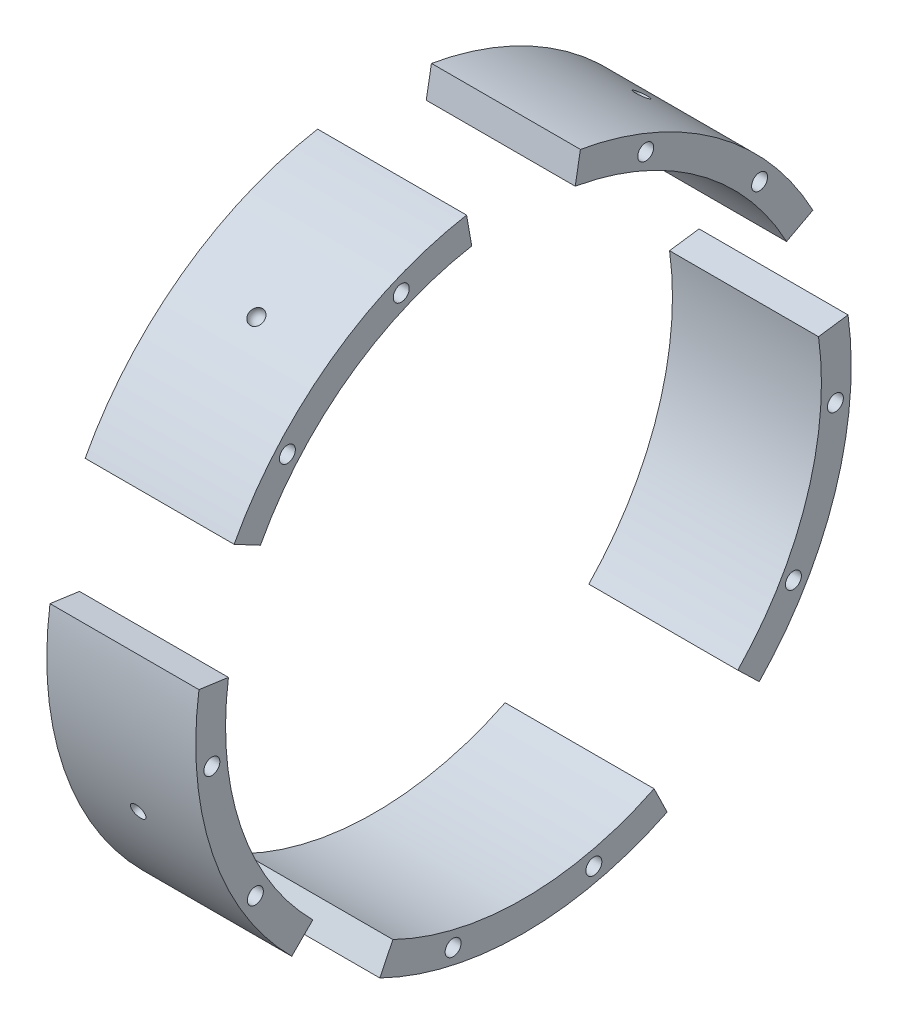
SolidWorks part; units mm, degrees
ref_plane "Front Plane" through (0, 0, 0) normal (0, 0, 1) x (1, 0, 0)
ref_plane "Top Plane" through (0, 0, 0) normal (0, 1, 0) x (1, 0, 0)
ref_plane "Right Plane" through (0, 0, 0) normal (1, 0, 0) x (0, 0, -1)
sketch "Sketch1" plane through (0, 0, 0) normal (1, 0, 0) x (0, 0, -1)
  line L1 (87.6742, -179.7588) -> (96.4417, -197.7347)
  line L2 (143.868, -138.9317) -> (158.2548, -152.8248)
  line L4 (198.0536, 27.8346) -> (217.859, 30.6181)
  line L5 (176.5895, 93.8943) -> (194.2485, 103.2837)
  line L7 (34.7296, 196.9616) -> (38.2026, 216.6577)
  line L8 (-34.7296, 196.9616) -> (-38.2026, 216.6577)
  line L10 (-176.5895, 93.8943) -> (-194.2485, 103.2837)
  line L11 (-198.0536, 27.8346) -> (-217.859, 30.6181)
  line L13 (-141.4214, -141.4214) -> (-155.5635, -155.5635)
  line L14 (-87.6742, -179.7588) -> (-96.4417, -197.7347)
  arc A0 (143.868, -138.9317) -> (198.0536, 27.8346) centre (0, 0) ccw
  arc A1 (158.2548, -152.8248) -> (217.859, 30.6181) centre (0, 0) ccw
  arc A2 (194.2485, 103.2837) -> (38.2026, 216.6577) centre (0, 0) ccw
  arc A3 (176.5895, 93.8943) -> (34.7296, 196.9616) centre (0, 0) ccw
  arc A4 (-38.2026, 216.6577) -> (-194.2485, 103.2837) centre (0, 0) ccw
  arc A5 (-34.7296, 196.9616) -> (-176.5895, 93.8943) centre (0, 0) ccw
  arc A6 (-198.0536, 27.8346) -> (-141.4214, -141.4214) centre (0, 0) ccw
  arc A7 (-217.859, 30.6181) -> (-155.5635, -155.5635) centre (0, 0) ccw
  arc A8 (-87.6742, -179.7588) -> (87.6742, -179.7588) centre (0, 0) ccw
  arc A9 (-96.4417, -197.7347) -> (96.4417, -197.7347) centre (0, 0) ccw
  point P8 (0, -220)
  point P11 (-208.6312, -69.807)
  point P14 (-129.3128, 177.9837)
  point P17 (129.3128, 177.9837)
  point P19 (209.2324, -67.9837)
  point P26 (87.6742, -179.7588)
  point P27 (143.868, -138.9317)
  point P29 (198.0536, 27.8346)
  point P30 (176.5895, 93.8943)
  point P32 (34.7296, 196.9616)
  point P33 (-34.7296, 196.9616)
extrude "Boss-Extrude1" add sketch "Sketch1" along normal blind 100
ref_plane "Plane1" through (0, 177.9837, 129.3128) normal (0, 0.809, 0.5878) x (1, 0, 0)
ref_plane "Plane2" through (0, -69.807, 208.6312) normal (0, -0.3173, 0.9483) x (1, 0, 0)
ref_plane "Plane3" through (0, -67.9837, -209.2324) normal (0, -0.309, -0.9511) x (-1, 0, 0)
ref_plane "Plane4" through (0, -220, 0) normal (0, -1, 0) x (-1, 0, 0)
ref_plane "Plane5" through (0, 177.9837, -129.3128) normal (0, 0.809, -0.5878) x (1, 0, 0)
sketch "Sketch2" plane through (0, 177.9837, 129.3128) normal (0, 0.809, 0.5878) x (1, 0, 0)
  line L0 (45, 0) -> (55, 0)
  arc A0 (55, 0) -> (45, 0) centre (50, 0) ccw
  point P6 (50, 0)
sketch "Sketch4" plane through (0, 177.9837, -129.3128) normal (0, 0.809, -0.5878) x (1, 0, 0)
  line L0 (45, 0) -> (55, 0)
  arc A0 (55, 0) -> (45, 0) centre (50, 0) ccw
  point P6 (50, 0)
sketch "Sketch5" plane through (0, -67.9837, -209.2324) normal (0, -0.309, -0.9511) x (-1, 0, 0)
  line L0 (-55, 0) -> (-45, 0)
  arc A0 (-45, 0) -> (-55, 0) centre (-50, 0) ccw
  point P5 (-50, 0)
sketch "Sketch6" plane through (0, -220, 0) normal (0, -1, 0) x (-1, 0, 0)
  line L0 (-55, 0) -> (-45, 0)
  arc A0 (-45, 0) -> (-55, 0) centre (-50, 0) cw
  point P5 (-50, 0)
sketch "Sketch7" plane through (0, -69.807, 208.6312) normal (0, -0.3173, 0.9483) x (1, 0, 0)
  line L0 (45, 0) -> (55, 0)
  arc A0 (55, 0) -> (45, 0) centre (50, 0) ccw
  point P5 (50, 0)
revolve "Cut-Revolve1" cut sketch "Sketch2" angle 360 about L0
revolve "Cut-Revolve2" cut sketch "Sketch4" angle 360 about L0
revolve "Cut-Revolve3" cut sketch "Sketch5" angle 360 about L0
revolve "Cut-Revolve4" cut sketch "Sketch6" angle 360 about L0
revolve "Cut-Revolve5" cut sketch "Sketch7" angle 360 about L0
ref_plane "Plane6" through (110, 0, 0) normal (1, 0, 0) x (0, 0, -1)
sketch "Sketch8" plane through (110, 0, 0) normal (1, 0, 0) x (0, 0, -1)
  line L0 (-129.3128, 177.9837) -> (-117.5571, 161.8034)
  line L1 (117.5571, 161.8034) -> (129.3128, 177.9837)
  line L2 (-190.2113, -61.8034) -> (-209.2324, -67.9837)
  line L3 (190.2113, -61.8034) -> (209.2324, -67.9837)
  line L4 (0, -200) -> (0, -220)
  line L5 (-150.9419, 131.2118) -> (-166.0361, 144.333)
  line L6 (-78.1462, 184.101) -> (-85.9608, 202.5111)
  line L7 (150.9419, 131.2118) -> (166.0361, 144.333)
  line L8 (78.1462, 184.101) -> (85.9608, 202.5111)
  line L9 (199.3447, -16.1766) -> (219.4045, -16.1766)
  line L10 (172.2044, -100.0777) -> (190.2113, -110.5426)
  line L11 (44.9902, -194.874) -> (49.4892, -214.3614)
  line L12 (-44.9902, -194.874) -> (-49.4892, -214.3614)
  line L13 (-171.4335, -103.0076) -> (-188.5768, -113.3084)
  line L14 (-199.2389, -17.4311) -> (-219.1628, -19.1743)
  arc A5 (-87.6742, -179.7588) -> (87.6742, -179.7588) centre (0, 0) ccw construction
  arc A6 (143.868, -138.9317) -> (198.0536, 27.8346) centre (0, 0) ccw construction
  arc A7 (176.5895, 93.8943) -> (34.7296, 196.9616) centre (0, 0) ccw construction
  arc A8 (-34.7296, 196.9616) -> (-176.5895, 93.8943) centre (0, 0) ccw construction
  arc A9 (-198.0536, 27.8346) -> (-141.4214, -141.4214) centre (0, 0) ccw construction
  circle A10 centre (0, 0) radius 220
  point P0 (-123.4349, 169.8936)
  point P1 (123.4349, 169.8936)
  point P3 (199.7219, -64.8936)
  point P5 (-117.5571, 161.8034)
  point P10 (117.5571, 161.8034)
  point P11 (190.2113, -61.8034)
  point P12 (0, -200)
  point P13 (-190.2113, -61.8034)
  point P19 (0, -210)
  point P20 (-199.7219, -64.8936)
  point P27 (-44.9902, -194.874)
  point P44 (-158.489, 137.7724)
  point P45 (-82.0535, 193.306)
  point P46 (82.0535, 193.306)
  point P47 (158.489, 137.7724)
  point P48 (209.3746, -16.1766)
  point P49 (44.9902, -194.874)
  point P53 (172.2044, -100.0777)
  point P54 (-171.4335, -103.0076)
  point P55 (-199.2389, -17.4311)
  point P59 (-150.9419, 131.2118)
  point P60 (-78.1462, 184.101)
  point P64 (78.1462, 184.101)
  point P65 (150.9419, 131.2118)
  point P69 (199.3447, -16.1766)
  point P70 (181.2078, -105.3102)
  point P74 (47.2397, -204.6177)
  point P75 (-47.2397, -204.6177)
  point P76 (-180.0051, -108.158)
  point P77 (-209.2009, -18.3027)
hole_wizard "1/2-13 Tapped Hole3" positions "3DSketch4" profile "Sketch13" tap size "1/2-13" standard "ANSI Inch"
sketch3d "3DSketch4"
  point P0 (110, 137.7724, 158.489)
  point P3 (110, 193.306, 82.0535)
  point P6 (110, -18.3027, 209.2009)
  point P9 (110, -108.158, 180.0051)
  point P12 (110, -204.6177, 47.2397)
  point P15 (110, -204.6177, -47.2397)
  point P18 (110, -105.3102, -181.2078)
  point P21 (110, -16.1766, -209.3746)
  point P24 (110, 137.7724, -158.489)
  point P27 (110, 193.306, -82.0535)
sketch "Sketch13" plane through (110, 137.7724, 158.489) normal (0, 1, 0) x (0, 0, -1)
  line L0 (0, 0) -> (0, 69.1195)
  line L1 (0, 69.1195) -> (5.3581, 65.9)
  line L2 (5.3581, 65.9) -> (5.3581, 0)
  line L5 (5.3581, 0) -> (0, 0)
  line L10 (0, 69.1195) -> (-5.3581, 65.9) construction
  line L11 (0, -6.35) -> (0, 107.95) construction
  dimension "Tap Drill Dia." = 10.7163
  dimension "Tap Drill Depth" = 65.9
  dimension "Drill Angle" = 118
